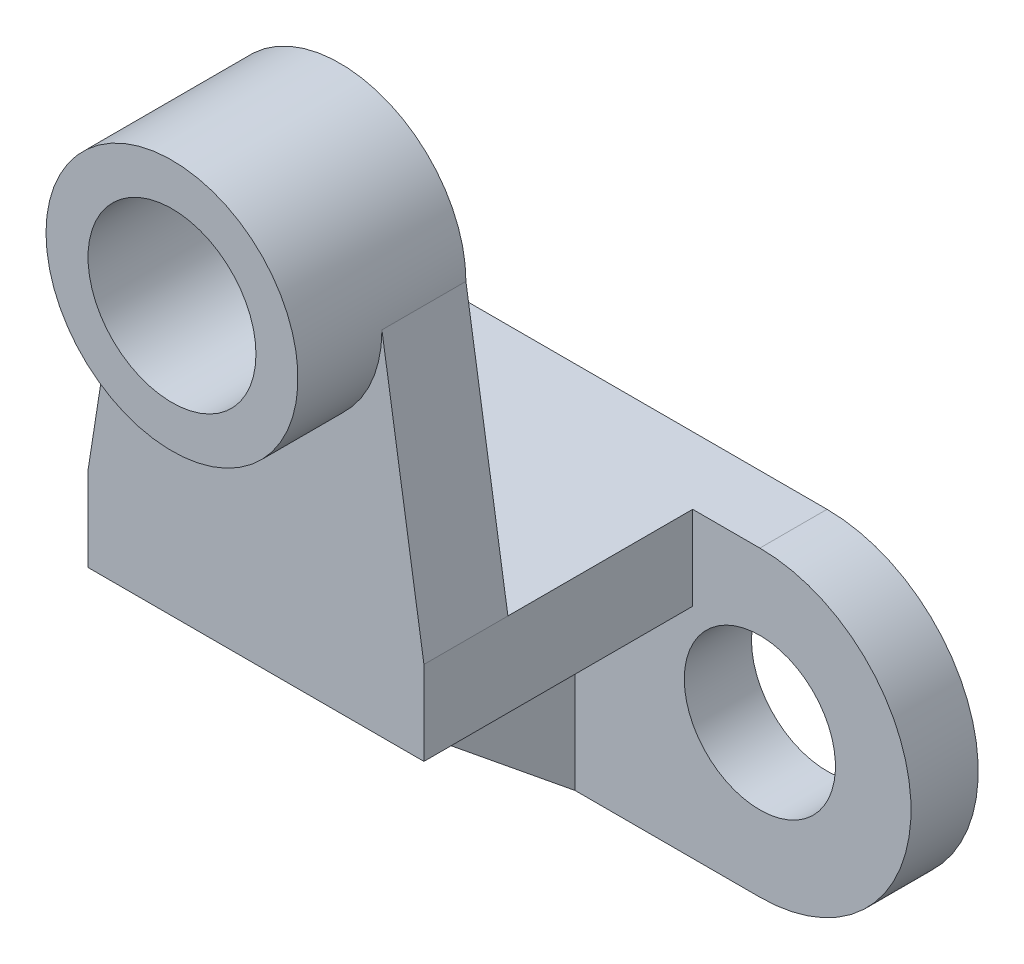
SolidWorks part; units mm, degrees
ref_plane "Front Plane" through (0, 0, 0) normal (0, 0, 1) x (1, 0, 0)
ref_plane "Top Plane" through (0, 0, 0) normal (0, 1, 0) x (1, 0, 0)
ref_plane "Right Plane" through (0, 0, 0) normal (1, 0, 0) x (0, 0, -1)
sketch "Sketch1" plane through (0, 0, 0) normal (0, 0, 1) x (1, 0, 0)
  line L0 (0, 0) -> (56, 0)
  line L2 (56, 36) -> (0, 36)
  arc A0 (0, 0) -> (0, 36) centre (0, 18) cw
  arc A1 (56, 0) -> (56, 36) centre (56, 18) ccw
  circle A2 centre (56, 18) radius 8
  circle A3 centre (0, 18) radius 8
  dimension "D2" = 18
  dimension "D3" = 16
  dimension "D1" = 56
extrude "Boss-Extrude2" add sketch "Sketch1" along normal blind 8 contours L2 A0 L0 A1
sketch "Sketch5" plane through (0, 0, 0) normal (0, 0, -1) x (-1, 0, 0)
  circle A0 centre (0, 18) radius 9
  circle A2 centre (-56, 18) radius 9
  dimension "D1" = 18
  dimension "D4" = 18
  dimension "D2" = 18
  dimension "D3" = 18
  dimension "D5" = 56
  dimension "D6" = 18
extrude "Cut-Extrude2" cut sketch "Sketch5" against normal blind 8 contours A0 | A2
sketch "Sketch6" plane through (0, 0, 8) normal (0, 0, 1) x (1, 0, 0)
  line L0 (8, 36) -> (48, 36)
  line L1 (56, 36) -> (0, 36) construction
  line L2 (48, 36) -> (48, 26)
  line L3 (48, 26) -> (34, 26)
  line L4 (34, 26) -> (34, 0)
  line L5 (0, 0) -> (56, 0) construction
  line L6 (34, 0) -> (22, 0)
  line L7 (22, 0) -> (22, 26)
  line L8 (22, 26) -> (8, 26)
  line L9 (8, 26) -> (8, 36)
  dimension "D1" = 40
  dimension "D2" = 10
  dimension "D3" = 10
  dimension "D4" = 12
  dimension "D5" = 14
  dimension "D6" = 22
extrude "Boss-Extrude3" add sketch "Sketch6" along normal blind 32
sketch "Sketch7" plane through (34, 0, 0) normal (1, 0, 0) x (0, 0, -1)
  line L0 (-40, 26) -> (-8, 0)
  line L1 (-40, 0) -> (-40, 26) construction
  line L2 (-40, 26) -> (-8, 26) construction
  line L3 (-8, 0) -> (-40, 0)
  line L4 (-40, 0) -> (-40, 26)
extrude "Cut-Extrude3" cut sketch "Sketch7" against normal blind 12
sketch "Sketch8" plane through (0, 36, 0) normal (0, 1, 0) x (1, 0, 0)
  line L0 (8, -40) -> (48, -40)
  line L1 (48, -40) -> (48, -30)
  line L2 (48, -40) -> (48, -8) construction
  line L3 (48, -30) -> (8, -30)
  line L4 (8, -40) -> (8, -8) construction
  line L5 (8, -30) -> (8, -40)
  dimension "D1" = 10
extrude "Boss-Extrude4" add sketch "Sketch8" along normal blind 32
sketch "Sketch10" plane through (0, 0, 30) normal (0, 0, -1) x (-1, 0, 0)
  line L0 (-48, 68) -> (-8, 68) construction
  circle A0 centre (-28, 68) radius 15
  dimension "D1" = 30
extrude "Boss-Extrude5" add sketch "Sketch10" against normal blind 20
sketch "Sketch11" plane through (0, 0, 40) normal (0, 0, 1) x (1, 0, 0)
  line L0 (43, 68) -> (48, 36)
  line L1 (48, 26) -> (48, 68) construction
  line L2 (48, 36) -> (48, 68)
  line L3 (48, 68) -> (43, 68)
  dimension "D1" = 0
extrude "Cut-Extrude4" cut sketch "Sketch11" against normal blind 10
sketch "Sketch13" plane through (0, 0, 40) normal (0, 0, 1) x (1, 0, 0)
  line L0 (13, 68) -> (8, 36)
  line L1 (8, 68) -> (8, 26) construction
  line L2 (8, 36) -> (8, 68)
  line L3 (8, 68) -> (13, 68)
  dimension "D1" = 0
extrude "Cut-Extrude5" cut sketch "Sketch13" against normal blind 10
sketch "Sketch14" plane through (0, 0, 50) normal (0, 0, 1) x (1, 0, 0)
  circle A0 centre (28, 68) radius 10
  circle A1 centre (28, 68) radius 15 construction
  dimension "D1" = 20
  dimension "D2" = 0
extrude "Cut-Extrude6" cut sketch "Sketch14" against normal blind 20
